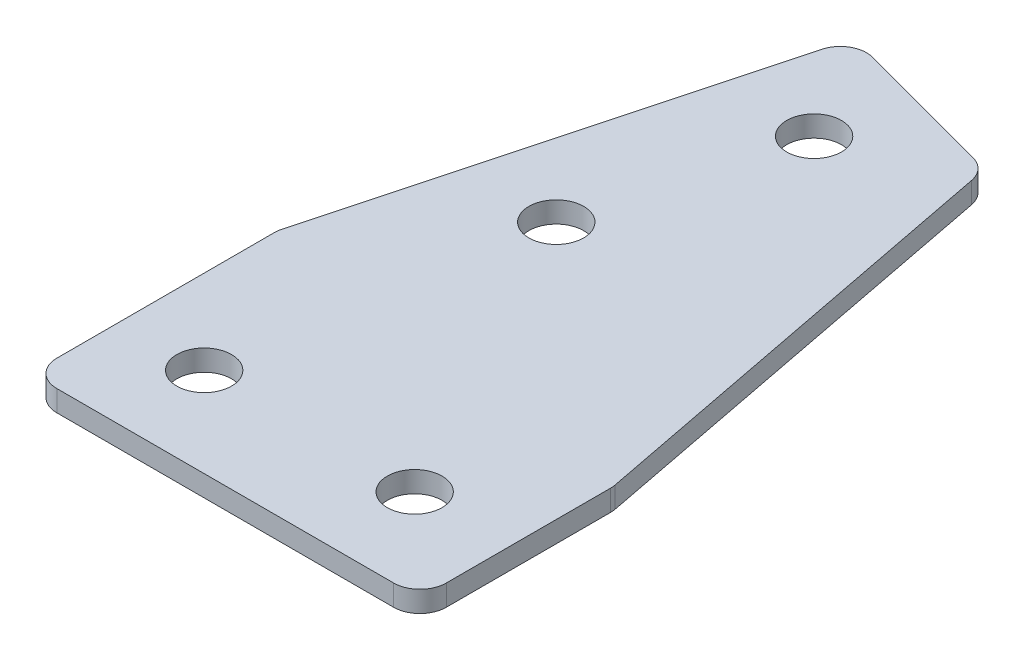
SolidWorks part; units mm, degrees
material "Сталь лист 2 мм"
ref_plane "Спереди" through (0, 0, 0) normal (0, 0, 1) x (1, 0, 0)
ref_plane "Сверху" through (0, 0, 0) normal (0, 1, 0) x (1, 0, 0)
ref_plane "Справа" through (0, 0, 0) normal (1, 0, 0) x (0, 0, -1)
sketch "Эскиз1" plane through (0, 0, 0) normal (0, 1, 0) x (1, 0, 0)
  line L0 (10, 500) -> (10, -500) construction
  line L1 (10, 500) -> (-10, 500) construction
  line L2 (10, -500) -> (-10, -500) construction
  line L3 (-10, 500) -> (-10, -500) construction
  line L4 (10, 500) -> (-10, -500) construction
  line L5 (10, -500) -> (-10, 500) construction
  line L6 (0, 500) -> (0, -500) construction
  line L7 (500, 10) -> (-500, 10) construction
  line L8 (500, 10) -> (500, -10) construction
  line L9 (-500, 10) -> (-500, -10) construction
  line L10 (500, -10) -> (-500, -10) construction
  line L11 (500, 10) -> (-500, -10) construction
  line L12 (-500, 10) -> (500, -10) construction
  line L13 (-139.0688, -480.3747) -> (119.7503, 485.5511) construction
  line L14 (-139.0688, -480.3747) -> (-119.7503, -485.5511) construction
  line L15 (119.7503, 485.5511) -> (139.0688, 480.3747) construction
  line L16 (-119.7503, -485.5511) -> (139.0688, 480.3747) construction
  line L17 (-139.0688, -480.3747) -> (139.0688, 480.3747) construction
  line L18 (119.7503, 485.5511) -> (-119.7503, -485.5511) construction
  line L19 (-129.4095, -482.9629) -> (129.4095, 482.9629) construction
  line L20 (-500, 0) -> (500, 0) construction
  point P1 (0, 0)
  point P9 (0, 0)
  point P10 (0, 0)
  dimension "D1" = 20
  dimension "D2" = 1000
  dimension "D3" = 20
  dimension "D4" = 20
  dimension "D5" = 1000
  dimension "D6" = 75
sketch "Эскиз2" plane through (0, 0, 0) normal (0, 1, 0) x (1, 0, 0)
  line L0 (33.7137, -10) -> (33.7137, 10)
  line L1 (33.7137, 10) -> (25.0427, 54.8236)
  line L5 (500, -10) -> (-500, -10) construction
  line L7 (-6.2863, -10) -> (33.7137, -10)
  line L10 (25.0427, 54.8236) -> (5.7242, 60)
  line L11 (-139.0688, -480.3747) -> (119.7503, 485.5511) construction
  line L12 (5.7242, 60) -> (-6.2863, 15.1764)
  line L14 (-6.2863, 15.1764) -> (-6.2863, -10)
  line L17 (-119.7503, -485.5511) -> (139.0688, 480.3747) construction
  line L20 (13.0323, 10) -> (-6.2863, 15.1764) construction
  line L21 (500, 10) -> (-500, 10) construction
  dimension "D1" = 70
  dimension "D2" = 40
extrude "Бобышка-Вытянуть1" add sketch "Эскиз2" along normal blind 2
sketch "Эскиз7" plane through (0, 2, 0) normal (0, 1, 0) x (1, 0, 0)
  line L6 (32.2137, -8.5) -> (32.2137, 9.8562)
  line L7 (32.2137, -8.5) -> (32.2137, 9.8562)
  line L8 (32.2137, 9.8562) -> (23.7482, 53.6176)
  line L9 (32.2137, 9.8562) -> (23.7482, 53.6176)
  line L10 (-4.7863, 14.9789) -> (-4.7863, -8.5)
  line L11 (-4.7863, -8.5) -> (32.2137, -8.5)
  line L13 (23.7482, 53.6176) -> (6.7848, 58.1629)
  line L14 (6.7848, 58.1629) -> (-4.7863, 14.9789)
  line L15 (-4.7863, 14.9789) -> (-4.7863, -8.5)
  line L16 (-4.7863, -8.5) -> (32.2137, -8.5)
  line L18 (23.7482, 53.6176) -> (6.7848, 58.1629)
  line L19 (6.7848, 58.1629) -> (-4.7863, 14.9789)
  dimension "D1" = 1.5
extrude "Вырез-Вытянуть5" cut sketch "Эскиз7" against normal through all flip side to cut
sketch "Эскиз3" plane through (0, 2, 0) normal (0, 1, 0) x (1, 0, 0)
  line L0 (-500, 0) -> (500, 0) construction
  line L1 (10, 500) -> (10, -500) construction
  line L2 (-4.7863, 14.9789) -> (-4.7863, -8.5) construction
  line L3 (-129.4095, -482.9629) -> (129.4095, 482.9629) construction
  line L5 (3.2137, 0) -> (23.2137, 0) construction
  line L6 (7.7483, 28.917) -> (12.9247, 48.2355) construction
  line L7 (23.2137, 0) -> (43.2137, 0) construction
  line L8 (500, 10) -> (-500, 10) construction
  line L10 (23.7482, 53.6176) -> (6.7848, 58.1629) construction
  line L11 (3.2137, 0) -> (-4.7863, 0) construction
  circle A1 centre (3.2137, 0) radius 2.6
  circle A2 centre (7.7483, 28.917) radius 2.6
  circle A3 centre (12.9247, 48.2355) radius 2.6
  circle A4 centre (23.2137, 0) radius 2.6
  circle A5 centre (43.2137, 0) radius 2.6
  point P18 (10, 10)
  dimension "D1" = 5.2
  dimension "D3" = 8
  dimension "D2" = 20
  dimension "D4" = 8
extrude "Вырез-Вытянуть1" cut sketch "Эскиз3" against normal through all
fillet "Скругление1" radius 2.5 6 edges at (-4.7863, 1, -14.9789) (-4.7863, 1, 8.5) (6.7848, 1, -58.1629) (32.2137, 1, 8.5) (32.2137, 1, -9.8562) (23.7482, 1, -53.6176)
